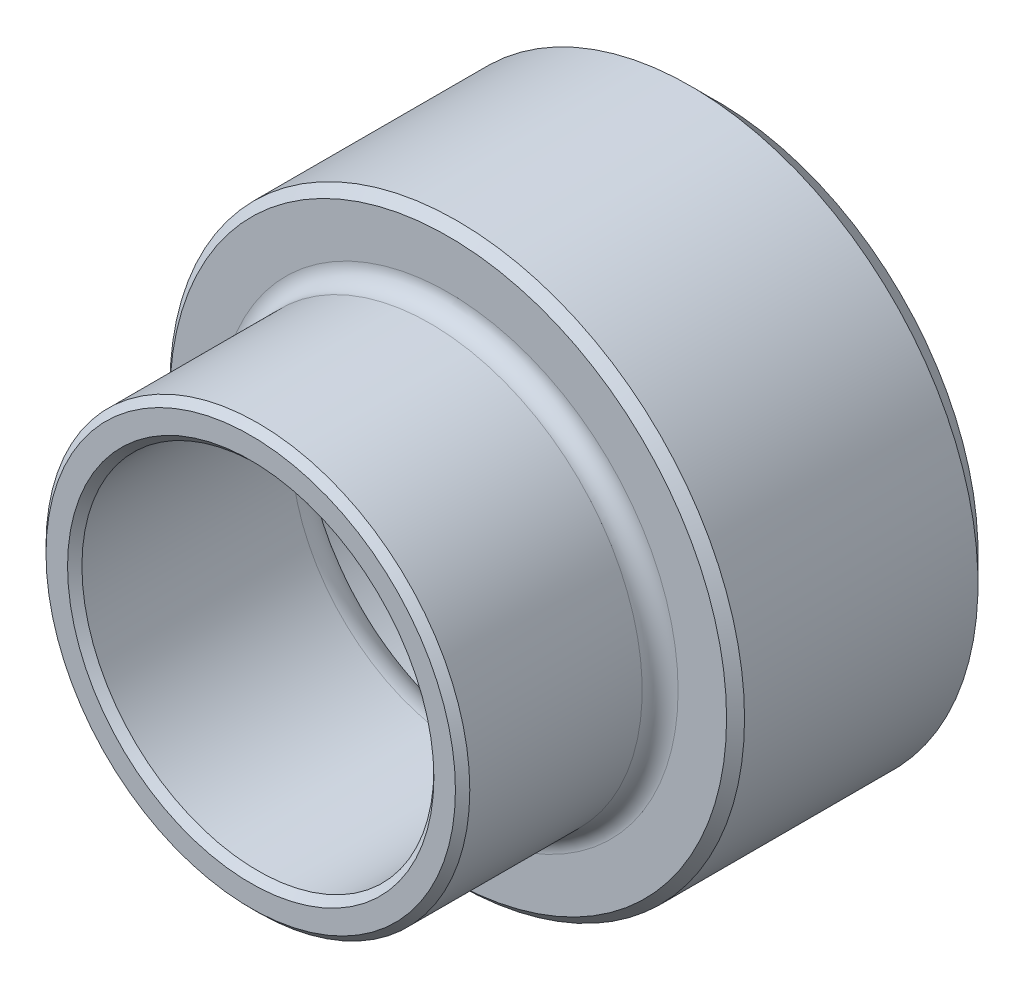
SolidWorks part; units mm, degrees
material "Brass"
ref_plane "Front" through (0, 0, 0) normal (0, 0, 1) x (1, 0, 0)
ref_plane "Top" through (0, 0, 0) normal (0, 1, 0) x (1, 0, 0)
ref_plane "Right" through (0, 0, 0) normal (1, 0, 0) x (0, 0, -1)
ref_plane "Plane1" through (0, 0, 0) normal (0, -1, 0) x (1, 0, 0)
sketch "Sketch1" plane through (0, 0, 0) normal (0, -1, 0) x (1, 0, 0)
  line L0 (5.9, 13) -> (4.9, 13)
  line L1 (4.9, 13) -> (4.9, 5.75)
  line L2 (4.9, 5.75) -> (0, 5.75)
  line L3 (0, 5.75) -> (0, 0)
  line L4 (0, 0) -> (8, 0)
  line L5 (8, 0) -> (8, 7.5)
  line L6 (8, 7.5) -> (6.4, 7.5)
  line L7 (5.9, 8) -> (5.9, 13)
  line L8 (0, 13) -> (0, 0) construction
  line L10 (0, 5.75) -> (4.9, 5.75) construction
  line L11 (6.4, 7.5) -> (5.9, 7.5) construction
  line L12 (5.9, 7.5) -> (5.9, 8) construction
  line L14 (4.9, 5.75) -> (4.9, 0) construction
  line L15 (4.9, 13) -> (0, 13) construction
  arc A0 (6.4, 7.5) -> (5.9, 8) centre (6.4, 8) cw
  dimension "D9" = 0.5
  dimension "D1" = 11.8
  dimension "D2" = 9.8
  dimension "D3" = 16
  dimension "D4" = 5.75
  dimension "D7" = 13
  dimension "D8" = 5.5
revolve "Revolve1" add sketch "Sketch1" angle 360 about L8
hole_wizard "Ø12.0 (12) Diameter Hole1" positions "Sketch3" profile "Sketch2" hole size "Ø12.0" standard "ISO"
sketch "Sketch3" plane through (0, 0, 0) normal (0, 0, -1) x (-1, 0, 0)
  point P0 (0, 0)
sketch "Sketch2" plane through (0, 0, 0) normal (1, 0, 0) x (0, 1, 0)
  line L0 (0, 0) -> (0, 9.3552)
  line L1 (0, 9.3552) -> (6, 5.75)
  line L2 (6, 5.75) -> (6, 0)
  line L5 (6, 0) -> (0, 0)
  line L10 (0, 9.3552) -> (-6, 5.75) construction
  line L11 (0, -6.35) -> (0, 107.95) construction
  dimension "Hole Dia." = 12
  dimension "Hole Depth" = 5.75
  dimension "Drill Angle" = 118
chamfer "Chamfer1" distance 0.75 angle 45 1 edges at (-8, 0, 0)
chamfer "Chamfer2" distance 0.25 angle 45 1 edges at (-8, 0, 7.5)
chamfer "Chamfer3" distance 0.2 angle 45 3 edges at (-5.9, 0, 13) (-4.9, 0, 13) (-6, 0, 0)
fillet "Fillet1" radius 1 1 edges at (-4.9, 0, 6.4109)
